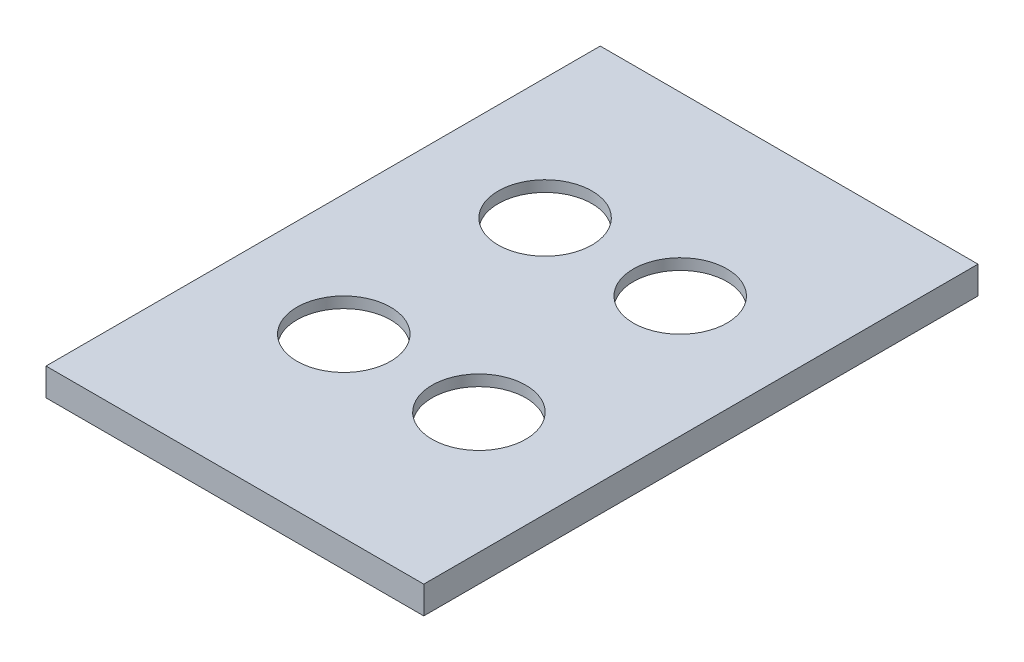
SolidWorks part; units mm, degrees
ref_plane "Alzado" through (0, 0, 0) normal (0, 0, 1) x (1, 0, 0)
ref_plane "Planta" through (0, 0, 0) normal (0, 1, 0) x (1, 0, 0)
ref_plane "Vista lateral" through (0, 0, 0) normal (1, 0, 0) x (0, 0, -1)
sketch "Croquis1" plane through (0, 0, 0) normal (0, 1, 0) x (1, 0, 0)
  line L1 (-24.5, 37) -> (40, 37)
  line L2 (-24.5, 37) -> (-24.5, -59.5)
  line L3 (-24.5, -59.5) -> (40, -59.5)
  line L4 (40, 37) -> (40, -59.5)
  line L6 (-6.25, -6.1) -> (-24.5, -6.1) construction
  line L7 (-4.5, -29.5) -> (20, -29.5) construction
  circle A0 centre (20, -29.5) radius 8.5
  circle A1 centre (-4.5, -29.5) radius 8.5
  circle A2 centre (-4.5, 7) radius 8.5
  circle A3 centre (20, 7) radius 8.5
  point P0 (0, 0)
  point P10 (0, -17.55)
  dimension "D8" = 30
  dimension "D16" = 17
  dimension "D17" = 17
  dimension "D18" = 20
  dimension "D10" = 30
  dimension "D11" = 30
  dimension "D13" = 20
  dimension "D14" = 17
  dimension "D15" = 17
  dimension "D9" = 20
  dimension "D19" = 20
  dimension "D12" = 64.5
  dimension "D20" = 96.5
  dimension "D22" = 23.4
extrude "Saliente-Extruir4" add sketch "Croquis1" along normal blind 2
sketch "Croquis2" plane through (0, 0, 0) normal (0, -1, 0) x (1, 0, 0)
  line L5 (-24.5, 59.5) -> (40, 59.5)
  line L6 (-24.5, 59.5) -> (-24.5, -37)
  line L7 (-24.5, -37) -> (40, -37)
  line L8 (42, -39) -> (42, 61.5)
  line L9 (42, 61.5) -> (-26.5, 61.5)
  line L10 (-26.5, 61.5) -> (-26.5, -39)
  line L11 (-26.5, -39) -> (42, -39)
  line L12 (42, -39) -> (42, 61.5)
  line L13 (42, 61.5) -> (-26.5, 61.5)
  line L14 (-26.5, 61.5) -> (-26.5, -39)
  line L15 (-26.5, -39) -> (42, -39)
  line L16 (40, 59.5) -> (40, -37)
  dimension "D1" = 2
extrude "Saliente-Extruir5" add sketch "Croquis2" along normal blind 3 and the other way up to surface (2 mm away) other way up to face at (-4.5, 2, 1.5)
